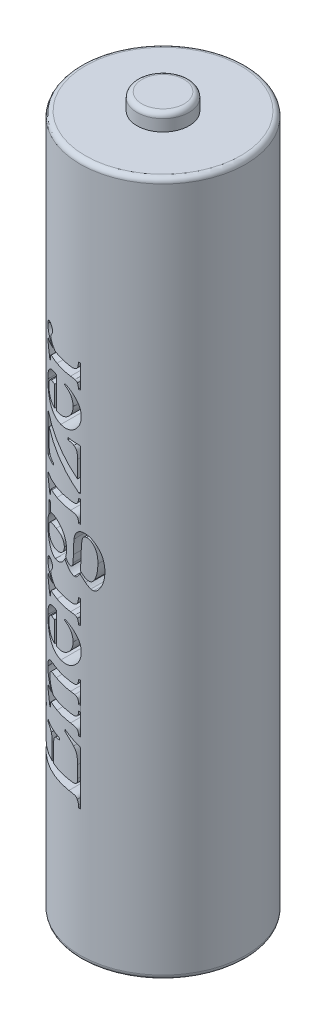
SolidWorks part; units mm, degrees
ref_plane "Front Plane" through (0, 0, 0) normal (0, 0, 1) x (1, 0, 0)
ref_plane "Top Plane" through (0, 0, 0) normal (0, 1, 0) x (1, 0, 0)
ref_plane "Right Plane" through (0, 0, 0) normal (1, 0, 0) x (0, 0, -1)
sketch "Sketch1" plane through (0, 0, 0) normal (0, 1, 0) x (1, 0, 0)
  circle A0 centre (0, 0) radius 5
  dimension "D1" = 10
extrude "Boss-Extrude1" add sketch "Sketch1" along normal blind 42
sketch "Sketch2" plane through (0, 42, 0) normal (0, 1, 0) x (1, 0, 0)
  circle A0 centre (0, 0) radius 1.575
  dimension "D1" = 3.15
extrude "Boss-Extrude2" add sketch "Sketch2" along normal blind 1
fillet "Fillet1" radius 0.3 3 edges at (0, 0, 5) (0, 42, 5) (0, 43, 1.575)
ref_plane "Plane1" through (0, 0, 30) normal (0, 0, 1) x (1, 0, 0)
sketch "Sketch6" plane through (0, 0, 30) normal (0, 0, 1) x (1, 0, 0)
  line L0 (0, 0) -> (0, 39.7824) construction
  text T0 "Energizer" font "Times New Roman" height in points 16
extrude "Cut-Extrude2" cut sketch "Sketch6" against normal blind 31
